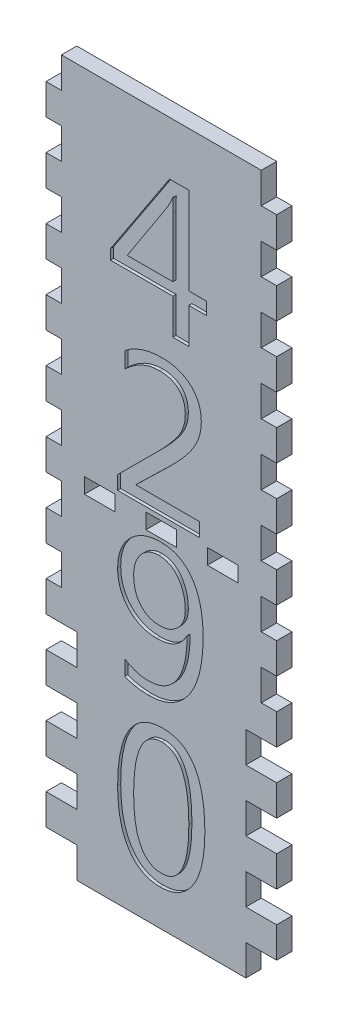
SolidWorks part; units mm, degrees
material "Pine"
ref_plane "Front Plane" through (0, 0, 0) normal (0, 0, 1) x (1, 0, 0)
ref_plane "Top Plane" through (0, 0, 0) normal (0, 1, 0) x (1, 0, 0)
ref_plane "Right Plane" through (0, 0, 0) normal (1, 0, 0) x (0, 0, -1)
sketch "Sketch1" plane through (0, 0, 0) normal (0, 0, 1) x (1, 0, 0)
  line L1 (0, 0) -> (95.25, 0)
  line L2 (0, 0) -> (0, 292.1)
  line L3 (0, 292.1) -> (95.25, 292.1)
  line L4 (95.25, 0) -> (95.25, 292.1)
  dimension "D1" = 95.25
  dimension "D2" = 292.1
extrude "Boss-Extrude1" add sketch "Sketch1" along normal blind 6.35
sketch "Sketch2" plane through (0, 0, 6.35) normal (0, 0, 1) x (1, 0, 0)
  line L0 (0, 292.1) -> (0, 0) construction
  line L1 (0, 0) -> (6.35, 0)
  line L2 (0, 0) -> (0, 12.7)
  line L3 (0, 12.7) -> (6.35, 12.7)
  line L4 (6.35, 0) -> (6.35, 12.7)
  line L5 (95.25, 0) -> (95.25, 292.1) construction
  line L6 (95.25, 0) -> (88.9, 0)
  line L7 (95.25, 0) -> (95.25, 12.7)
  line L8 (95.25, 12.7) -> (88.9, 12.7)
  line L9 (88.9, 0) -> (88.9, 12.7)
  dimension "D2" = 12.7
  dimension "D3" = 6.35
extrude "Cut-Extrude1" cut sketch "Sketch2" against normal through all
pattern_linear "LPattern1" count 12 spacing 25.4 along (0, 1, 0) of "Cut-Extrude1"
sketch "Sketch3" plane through (0, 0, 6.35) normal (0, 0, 1) x (1, 0, 0)
  line L0 (6.35, 0) -> (88.9, 0) construction
  line L1 (88.9, 12.7) -> (82.55, 12.7)
  line L2 (88.9, 12.7) -> (88.9, 0)
  line L3 (88.9, 0) -> (82.55, 0)
  line L4 (82.55, 12.7) -> (82.55, 0)
  line L5 (95.25, 12.7) -> (88.9, 12.7) construction
  line L6 (6.35, 12.7) -> (12.7, 12.7)
  line L7 (6.35, 12.7) -> (6.35, 0)
  line L8 (6.35, 0) -> (12.7, 0)
  line L9 (12.7, 12.7) -> (12.7, 0)
extrude "Cut-Extrude2" cut sketch "Sketch3" against normal through all
pattern_linear "LPattern2" count 4 spacing 25.4 along (0, 1, 0) of "Cut-Extrude2"
sketch "Sketch4" plane through (0, 0, 6.35) normal (0, 0, 1) x (1, 0, 0)
  line L0 (6.35, 139.7) -> (0, 139.7) construction
  line L1 (41.275, 146.05) -> (53.975, 146.05)
  line L2 (41.275, 146.05) -> (41.275, 139.7)
  line L3 (41.275, 139.7) -> (53.975, 139.7)
  line L4 (53.975, 146.05) -> (53.975, 139.7)
  line L5 (47.625, 139.7) -> (47.625, 0) construction
  line L6 (12.7, 0) -> (82.55, 0) construction
  dimension "D1" = 6.35
  dimension "D2" = 12.7
extrude "Cut-Extrude3" cut sketch "Sketch4" against normal through all
pattern_linear "LPattern3" count 2 spacing 25.4 along (-1, 0, 0) count 2 spacing 25.4 along (1, 0, 0) of "Cut-Extrude3"
sketch "Sketch5" plane through (0, 0, 6.35) normal (0, 0, 1) x (1, 0, 0)
  line L0 (25.908, 214.122) -> (25.908, -18.299) construction
  text T0 "<r90>4290</r>" font "Segoe UI" height 55.88
  dimension "D1" = 214.122
  dimension "D2" = 25.908
extrude "Cut-Extrude4" cut sketch "Sketch5" against normal blind 1.27
